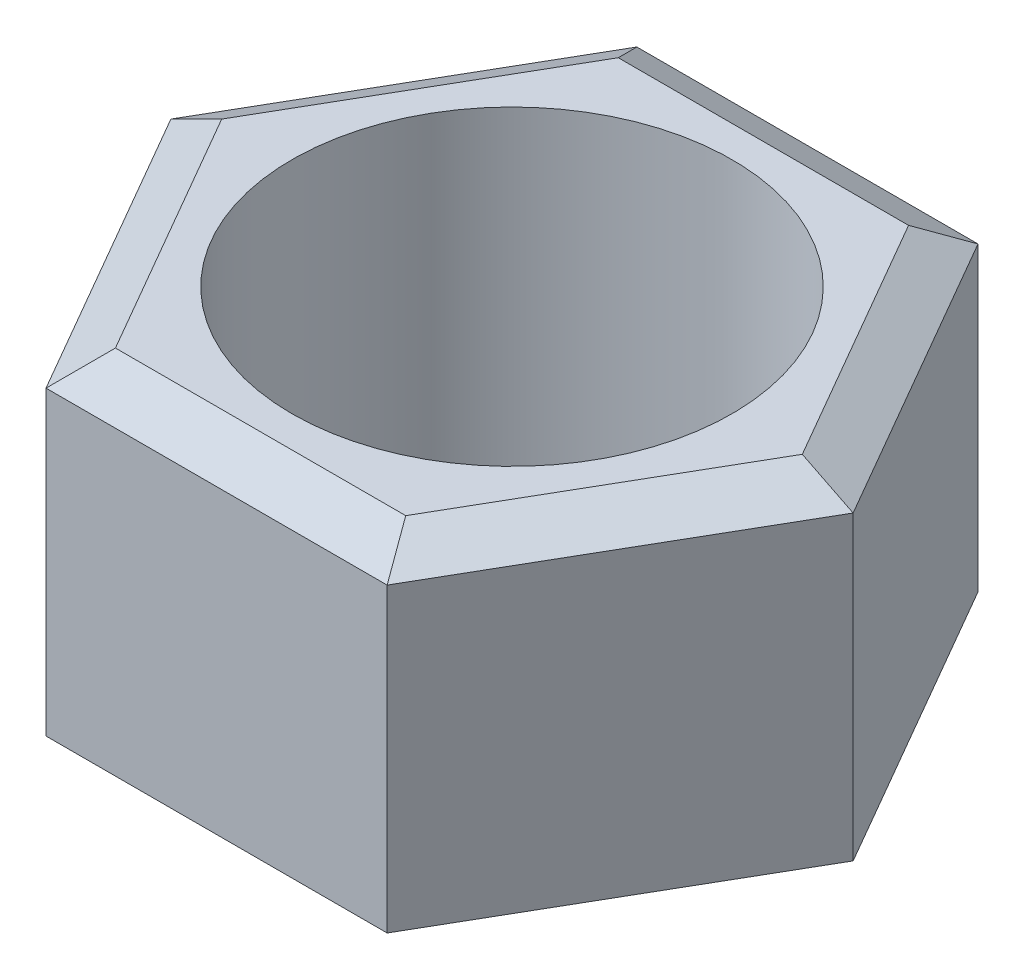
SolidWorks part; units mm, degrees
ref_plane "Спереди" through (0, 0, 0) normal (0, 0, 1) x (1, 0, 0)
ref_plane "Сверху" through (0, 0, 0) normal (0, 1, 0) x (1, 0, 0)
ref_plane "Справа" through (0, 0, 0) normal (1, 0, 0) x (0, 0, -1)
sketch "Эскиз1" plane through (0, 0, 0) normal (0, 1, 0) x (1, 0, 0)
  line L1 (-7.75, 0) -> (-3.875, -6.7117)
  line L2 (-3.875, -6.7117) -> (3.875, -6.7117)
  line L3 (3.875, -6.7117) -> (7.75, 0)
  line L4 (7.75, 0) -> (3.875, 6.7117)
  line L5 (3.875, 6.7117) -> (-3.875, 6.7117)
  line L6 (-3.875, 6.7117) -> (-7.75, 0)
  circle A0 centre (0, 0) radius 7.75 construction
  circle A1 centre (0, 0) radius 5
extrude "Бобышка-Вытянуть1" add sketch "Эскиз1" along normal blind 8
chamfer "Фаска1" distance 1 angle 30 6 edges at (5.8125, 8, -3.3558) (0, 8, -6.7117) (-5.8125, 8, -3.3558) (-5.8125, 8, 3.3558) (0, 8, 6.7117) (5.8125, 8, 3.3558)
chamfer "Фаска2" distance 1 angle 30 6 edges at (-5.8125, 0, -3.3558) (-5.8125, 0, 3.3558) (0, 0, 6.7117) (5.8125, 0, 3.3558) (5.8125, 0, -3.3558) (0, 0, -6.7117)
